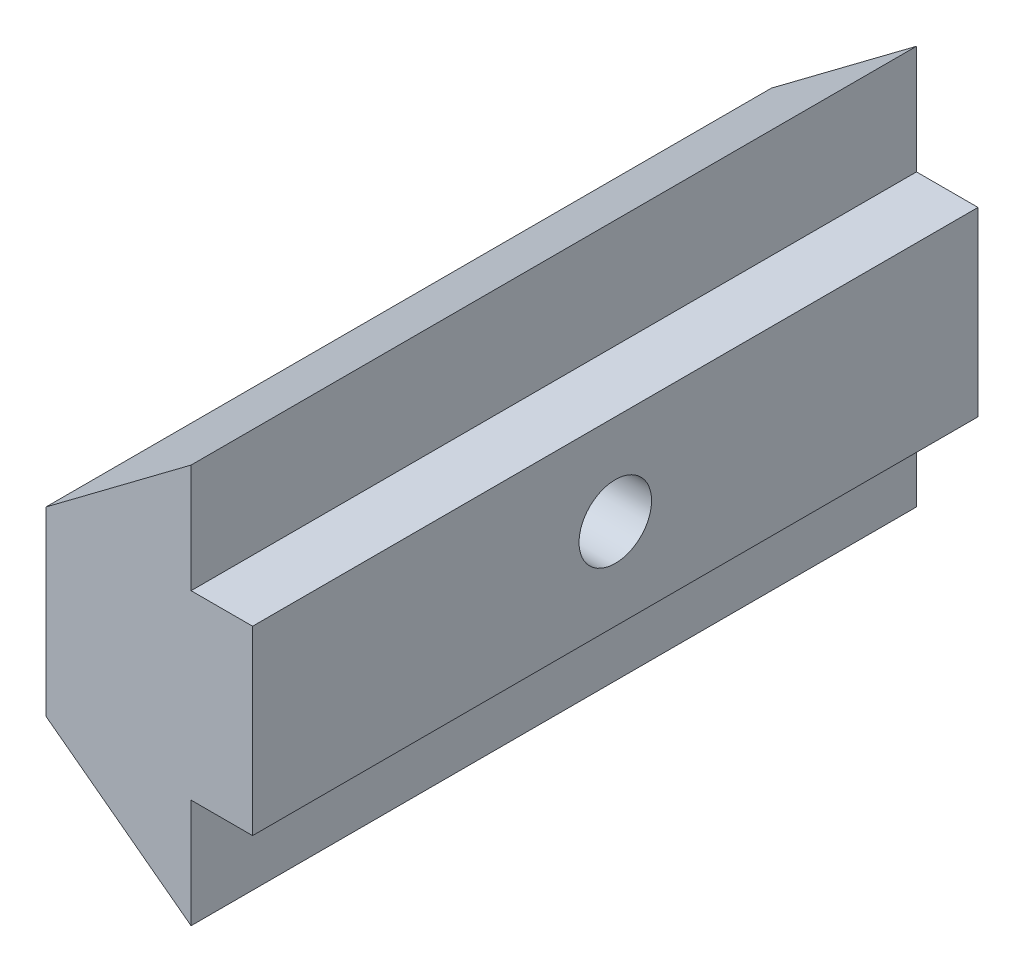
SolidWorks part; units mm, degrees
ref_plane "Plan de face" through (0, 0, 0) normal (0, 0, 1) x (1, 0, 0)
ref_plane "Plan de dessus" through (0, 0, 0) normal (0, 1, 0) x (1, 0, 0)
ref_plane "Plan de droite" through (0, 0, 0) normal (1, 0, 0) x (0, 0, -1)
sketch "ProfileRainureEsquisse" plane through (0, 0, 0) normal (0, 0, 1) x (1, 0, 0)
  line L0 (0, 0) -> (0, 5)
  line L1 (0, 5) -> (4, 8)
  line L2 (0, 0) -> (4, -3)
  line L3 (4, 8) -> (4, 5)
  line L4 (4, 5) -> (5.6958, 5)
  line L5 (5.6958, 5) -> (5.6958, 0)
  line L6 (5.6958, 0) -> (4, 0)
  line L7 (4, 0) -> (4, -3)
  dimension "D1" = 4
  dimension "D2" = 5.6958
  dimension "D3" = 5
  dimension "D4" = 8
extrude "Boss.-Extru.1" add sketch "ProfileRainureEsquisse" along normal blind 20
sketch "Esquisse1" plane through (5.6958, 0, 0) normal (1, 0, 0) x (0, 0, -1)
  line L0 (-20, 0) -> (-20, 5) construction
  circle A0 centre (-10, 2.5) radius 1
  point P2 (-20, 2.5)
  point P7 (-20, 2.5)
  point P10 (-20, 2.5)
  dimension "D1" = 2
  dimension "D2" = 10
extrude "Enlèv. mat.-Extru.1" cut sketch "Esquisse1" against normal through all
